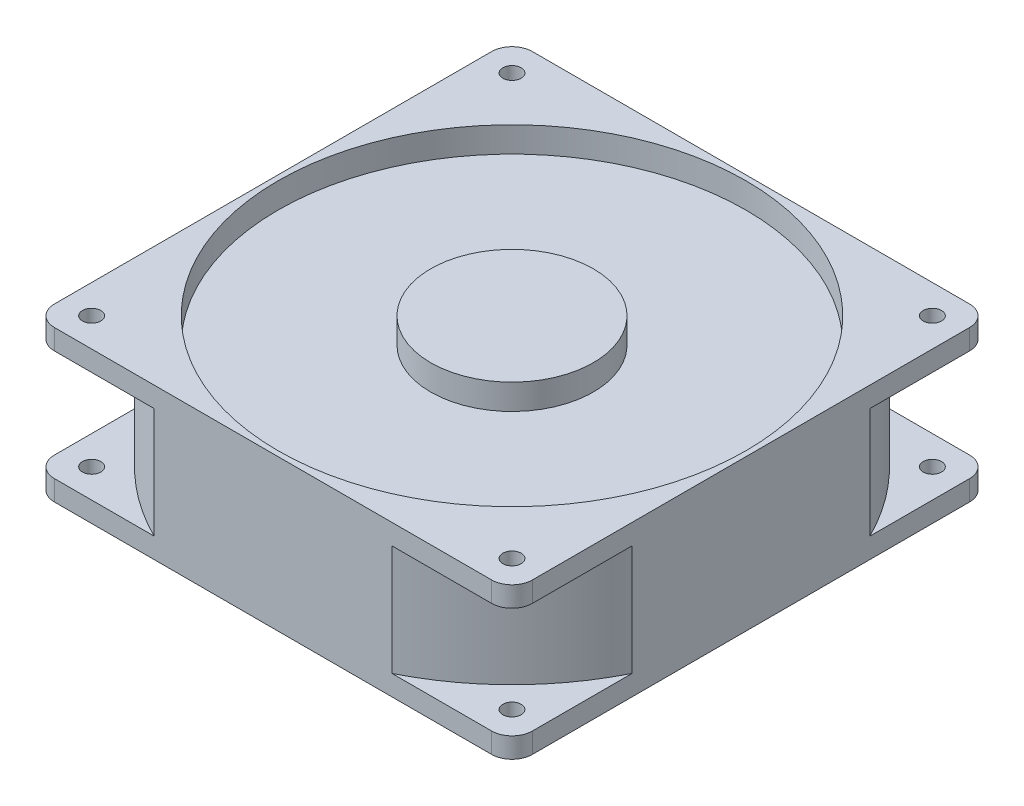
SolidWorks part; units mm, degrees
ref_plane "Front Plane" through (0, 0, 0) normal (0, 0, 1) x (1, 0, 0)
ref_plane "Top Plane" through (0, 0, 0) normal (0, 1, 0) x (1, 0, 0)
ref_plane "Right Plane" through (0, 0, 0) normal (1, 0, 0) x (0, 0, -1)
sketch "Sketch1" plane through (0, 0, 0) normal (0, 1, 0) x (1, 0, 0)
  line L1 (-116.7018, 111.0512) -> (2.6782, 111.0512)
  line L2 (-116.7018, 111.0512) -> (-116.7018, -8.3288)
  line L3 (-116.7018, -8.3288) -> (2.6782, -8.3288)
  line L4 (2.6782, 111.0512) -> (2.6782, -8.3288)
  line L5 (-116.7018, 111.0512) -> (2.6782, -8.3288) construction
  line L6 (-116.7018, -8.3288) -> (2.6782, 111.0512) construction
  point P0 (-57.0118, 51.3612)
  dimension "D1" = 119.38
  dimension "D2" = 119.38
extrude "Boss-Extrude1" add sketch "Sketch1" along normal blind 37.75
sketch "Sketch2" plane through (0, 37.75, 0) normal (0, 1, 0) x (1, 0, 0)
  line L0 (-57.0118, 111.0512) -> (-57.0118, -8.3288) construction
  line L1 (2.6782, 111.0512) -> (-116.7018, 111.0512) construction
  line L2 (-116.7018, -8.3288) -> (2.6782, -8.3288) construction
  line L3 (-116.7018, 51.3612) -> (2.6782, 51.3612) construction
  line L4 (-116.7018, 111.0512) -> (-116.7018, -8.3288) construction
  line L5 (2.6782, -8.3288) -> (2.6782, 111.0512) construction
  line L6 (-4.5118, -1.1388) -> (-109.5118, -1.1388) construction
  line L7 (-4.5118, -1.1388) -> (-4.5118, 103.8612) construction
  circle A0 centre (-109.5118, 103.8612) radius 2.286
  circle A1 centre (-4.5118, 103.8612) radius 2.286
  circle A2 centre (-4.5118, -1.1388) radius 2.286
  circle A3 centre (-109.5118, -1.1388) radius 2.286
  point P12 (-57.0118, 51.3612)
  point P21 (-57.0118, -1.1388)
  point P22 (-4.5118, 51.3612)
  dimension "D3" = 4.572
  dimension "D4" = 4.572
  dimension "D5" = 4.572
  dimension "D6" = 4.572
  dimension "D7" = 105
  dimension "D2" = 105
extrude "Cut-Extrude1" cut sketch "Sketch2" against normal through all
sketch "Sketch3" plane through (0, 37.75, 0) normal (0, 1, 0) x (1, 0, 0)
  line L0 (-116.7018, 51.3612) -> (2.6782, 51.3612) construction
  line L1 (-116.7018, 111.0512) -> (-116.7018, -8.3288) construction
  line L2 (2.6782, -8.3288) -> (2.6782, 111.0512) construction
  line L3 (-57.0118, -8.3288) -> (-57.0118, 111.0512) construction
  line L4 (-116.7018, -8.3288) -> (2.6782, -8.3288) construction
  line L5 (2.6782, 111.0512) -> (-116.7018, 111.0512) construction
  circle A0 centre (-57.0118, 51.3612) radius 58.4197
  dimension "D1" = 116.8395
extrude "Cut-Extrude2" cut sketch "Sketch3" against normal blind 6.35
sketch "Sketch4" plane through (0, 0, 0) normal (0, -1, 0) x (1, 0, 0)
  line L0 (-57.0118, -111.0512) -> (-57.0118, 8.3288) construction
  line L1 (2.6782, -111.0512) -> (-116.7018, -111.0512) construction
  line L2 (-116.7018, 8.3288) -> (2.6782, 8.3288) construction
  line L3 (2.6782, -51.3612) -> (-116.7018, -51.3612) construction
  line L4 (2.6782, 8.3288) -> (2.6782, -111.0512) construction
  line L5 (-116.7018, -111.0512) -> (-116.7018, 8.3288) construction
  circle A0 centre (-57.0118, -51.3612) radius 58.42
  dimension "D1" = 116.84
extrude "Cut-Extrude3" cut sketch "Sketch4" against normal blind 6.35
sketch "Sketch5" plane through (0, 6.35, 0) normal (0, -1, 0) x (1, 0, 0)
  circle A0 centre (-57.0118, -51.3612) radius 20.32
  dimension "D1" = 40.64
extrude "Boss-Extrude2" add sketch "Sketch5" along normal blind 6.35
sketch "Sketch6" plane through (0, 31.4, 0) normal (0, 1, 0) x (1, 0, 0)
  circle A0 centre (-57.0118, 51.3612) radius 20.32
extrude "Boss-Extrude3" add sketch "Sketch6" along normal blind 6.35
fillet "Fillet1" radius 5.08 4 edges at (2.6782, 18.875, 8.3288) (-116.7018, 18.875, 8.3288) (2.6782, 18.875, -111.0512) (-116.7018, 18.875, -111.0512)
ref_plane "Plane1" through (0, 18.875, 0) normal (0, 1, 0) x (1, 0, 0)
sketch "Sketch7" plane through (0, 18.875, 0) normal (0, 1, 0) x (1, 0, 0)
  circle A0 centre (-57.0118, 51.3612) radius 66.675
  circle A1 centre (-57.0118, 51.3612) radius 88.9
  dimension "D1" = 133.35
  dimension "D2" = 177.8
extrude "Cut-Extrude5" cut sketch "Sketch7" against normal mid plane 27.6
